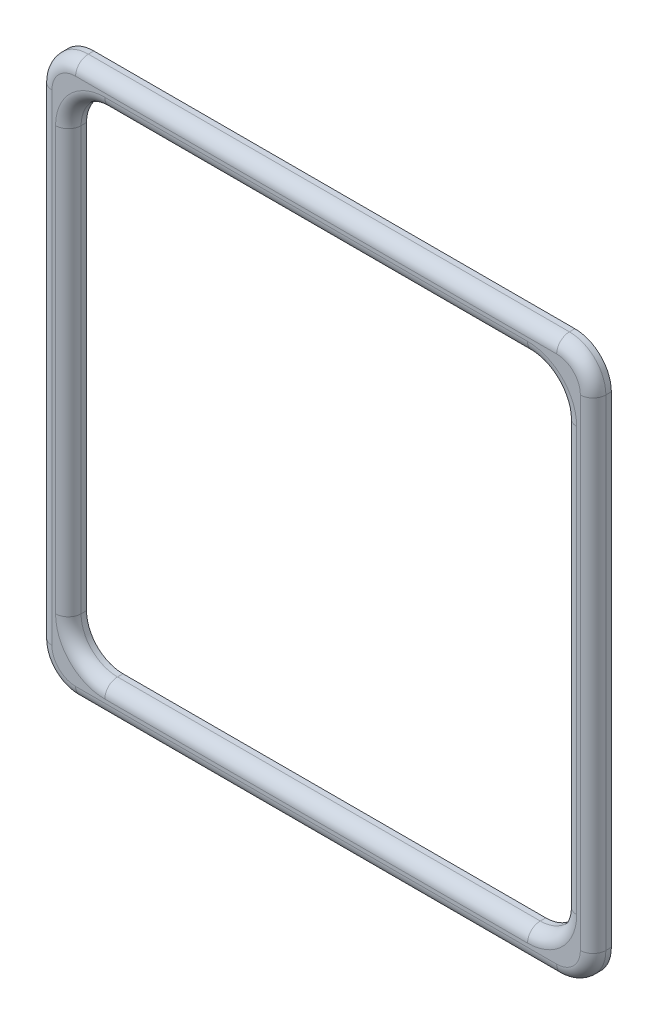
SolidWorks part; units mm, degrees
ref_plane "Front" through (0, 0, 0) normal (0, 0, 1) x (1, 0, 0)
ref_plane "Top" through (0, 0, 0) normal (0, 1, 0) x (1, 0, 0)
ref_plane "Right" through (0, 0, 0) normal (1, 0, 0) x (0, 0, -1)
sketch "Sketch1" plane through (0, 0, 0) normal (0, 0, 1) x (1, 0, 0)
  line L1 (29, 34) -> (-29, 34)
  line L2 (34, 29) -> (34, -29)
  line L3 (29, -34) -> (-29, -34)
  line L4 (-34, 29) -> (-34, -29)
  line L5 (34, 34) -> (-34, -34) construction
  line L6 (34, -34) -> (-34, 34) construction
  line L7 (-33, 38) -> (33, 38)
  line L8 (-38, 33) -> (-38, -33)
  line L9 (-33, -38) -> (33, -38)
  line L10 (38, 33) -> (38, -33)
  line L11 (-38, 38) -> (38, -38) construction
  line L12 (-38, -38) -> (38, 38) construction
  arc A0 (-38, -33) -> (-33, -38) centre (-33, -33) ccw
  arc A1 (-29, -34) -> (-34, -29) centre (-29, -29) cw
  arc A2 (34, -29) -> (29, -34) centre (29, -29) cw
  arc A3 (33, -38) -> (38, -33) centre (33, -33) ccw
  arc A4 (33, 38) -> (38, 33) centre (33, 33) cw
  arc A5 (29, 34) -> (34, 29) centre (29, 29) cw
  arc A6 (-33, 38) -> (-38, 33) centre (-33, 33) ccw
  arc A7 (-29, 34) -> (-34, 29) centre (-29, 29) ccw
  point P0 (0, 0)
  point P6 (0, 0)
  dimension "D5" = 5
  dimension "D1" = 68
  dimension "D2" = 68
  dimension "D3" = 76
  dimension "D4" = 76
extrude "Boss-Extrude1" add sketch "Sketch1" along normal blind 2.5
fillet "Fillet1" radius 1.75 16 edges at (-32.5355, 32.5355, 2.5) (0, 34, 2.5) (32.5355, 32.5355, 2.5) (34, 0, 2.5) (32.5355, -32.5355, 2.5) (0, -34, 2.5) (-32.5355, -32.5355, 2.5) (-36.5355, 36.5355, 2.5) (0, 38, 2.5) (36.5355, 36.5355, 2.5) (38, 0, 2.5) (36.5355, -36.5355, 2.5) (0, -38, 2.5) (-36.5355, -36.5355, 2.5) (-34, 0, 2.5) (-38, 0, 2.5)
